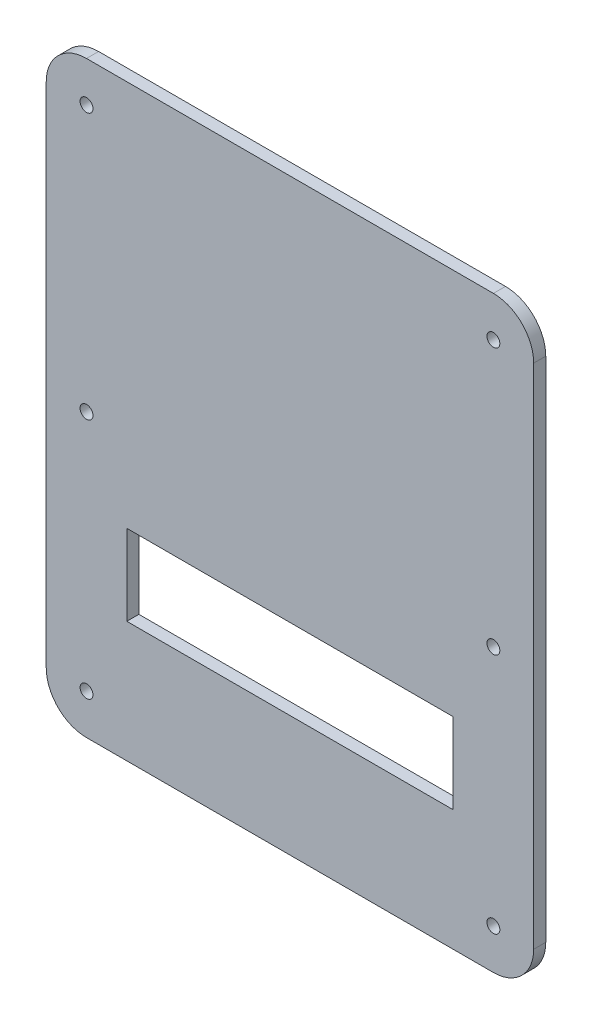
SolidWorks part; units mm, degrees
material "ｱｸﾘﾙ (中-上級の耐衝撃性)"
ref_plane "正面" through (0, 0, 0) normal (0, 0, 1) x (1, 0, 0)
ref_plane "平面" through (0, 0, 0) normal (0, 1, 0) x (1, 0, 0)
ref_plane "右側面" through (0, 0, 0) normal (1, 0, 0) x (0, 0, -1)
sketch "ｽｹｯﾁ1" plane through (0, 0, 0) normal (0, 0, 1) x (1, 0, 0)
  line L1 (0, 0) -> (121, 0)
  line L2 (0, 0) -> (0, 146)
  line L3 (0, 146) -> (121, 146)
  line L4 (121, 0) -> (121, 146)
extrude "ﾎﾞｽ - 押し出し1" add sketch "ｽｹｯﾁ1" along normal blind 3
fillet "ﾌｨﾚｯﾄ1" radius 10 4 edges at (121, 146, 1.5) (121, 0, 1.5) (0, 0, 1.5) (0, 146, 1.5)
sketch "ｽｹｯﾁ2" plane through (0, 0, 3) normal (0, 0, 1) x (1, 0, 0)
  line L0 (0, 25) -> (121, 25) construction
  line L1 (0, 136) -> (0, 10) construction
  line L2 (121, 10) -> (121, 136) construction
  line L3 (10, 0) -> (111, 0) construction
  line L4 (10, -889.6053) -> (10, 49110.3947) construction
  line L5 (111, -891.9006) -> (111, 49108.0994) construction
  line L6 (-954.0371, 136) -> (49045.9629, 136) construction
  line L7 (-944.8558, 70) -> (49055.1442, 70) construction
  line L8 (111, 146) -> (10, 146) construction
  line L9 (-911.0991, 10) -> (49088.9009, 10) construction
  line L10 (10, 0) -> (111, 0) construction
  circle A0 centre (10, 136) radius 1.6
  circle A1 centre (10, 70.0352) radius 1.6
  circle A2 centre (111, 136) radius 1.6
  circle A3 centre (111, 70) radius 1.6
  circle A4 centre (111, 10) radius 1.6
  circle A5 centre (10, 10) radius 1.6
  dimension "D6" = 10
  dimension "D1" = 25
  dimension "D2" = 10
  dimension "D3" = 66
  dimension "D4" = 10
  dimension "D5" = 101
extrude "ｶｯﾄ - 押し出し1" cut sketch "ｽｹｯﾁ2" against normal through all
sketch "ｽｹｯﾁ3" plane through (0, 0, 3) normal (0, 0, 1) x (1, 0, 0)
  line L0 (-974.695, 60) -> (49025.305, 60) construction
  line L1 (111, 146) -> (10, 146) construction
  line L2 (-974.3124, 50) -> (49025.6876, 50) construction
  line L3 (-974.1212, 30) -> (49025.8788, 30) construction
  line L4 (20, -942.2065) -> (20, 49057.7935) construction
  line L5 (101, -945.6495) -> (101, 49054.3505) construction
  line L6 (0, 136) -> (0, 10) construction
  line L7 (121, 10) -> (121, 136) construction
  line L9 (20, 50) -> (101, 50)
  line L10 (20, 50) -> (20, 30)
  line L11 (20, 30) -> (101, 30)
  line L12 (101, 50) -> (101, 30)
  dimension "D1" = 86
  dimension "D2" = 10
  dimension "D3" = 20
  dimension "D4" = 20
  dimension "D5" = 20
extrude "ｶｯﾄ - 押し出し2" cut sketch "ｽｹｯﾁ3" against normal through all
sketch "ﾍﾞﾝﾄﾞ-ﾗｲﾝ1" plane through (0, 0, 0) normal (0, 1, 0) x (1, 0, 0)
sketch "境界ﾎﾞｯｸｽ1" plane through (0, 0, 0) normal (0, 1, 0) x (1, 0, 0)
